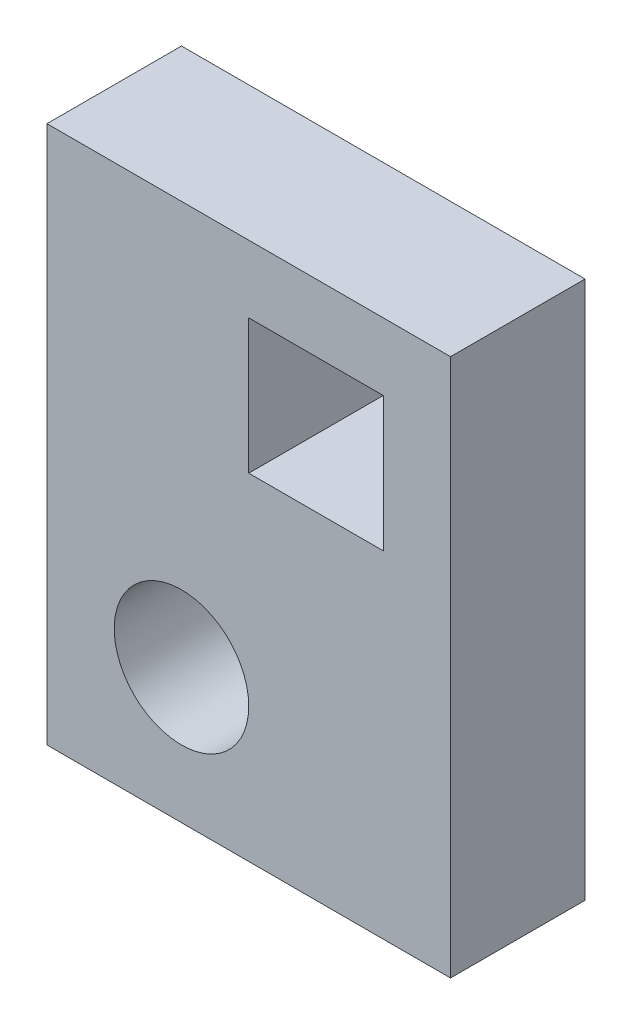
SolidWorks part; units mm, degrees
ref_plane "Front" through (0, 0, 0) normal (0, 0, 1) x (1, 0, 0)
ref_plane "Top" through (0, 0, 0) normal (0, 1, 0) x (1, 0, 0)
ref_plane "Right" through (0, 0, 0) normal (1, 0, 0) x (0, 0, -1)
sketch "Sketch1" plane through (0, 0, 0) normal (0, 0, 1) x (1, 0, 0)
  line L1 (0, 0) -> (76.2, 0)
  line L2 (0, 0) -> (0, 101.6)
  line L3 (0, 101.6) -> (76.2, 101.6)
  line L4 (76.2, 0) -> (76.2, 101.6)
  line L5 (38.1, 88.9) -> (63.5, 88.9)
  line L6 (38.1, 88.9) -> (38.1, 63.5)
  line L7 (38.1, 63.5) -> (63.5, 63.5)
  line L8 (63.5, 88.9) -> (63.5, 63.5)
  line L9 (38.1, 88.9) -> (63.5, 63.5) construction
  line L10 (38.1, 63.5) -> (63.5, 88.9) construction
  circle A0 centre (25.4, 25.4) radius 12.7
  point P7 (50.8, 76.2)
  dimension "D5" = 25.4
  dimension "D1" = 76.2
  dimension "D2" = 101.6
  dimension "D3" = 25.4
  dimension "D4" = 25.4
  dimension "D6" = 50.8
  dimension "D7" = 25.4
  dimension "D8" = 76.2
extrude "Boss-Extrude1" add sketch "Sketch1" along normal blind 25.4
